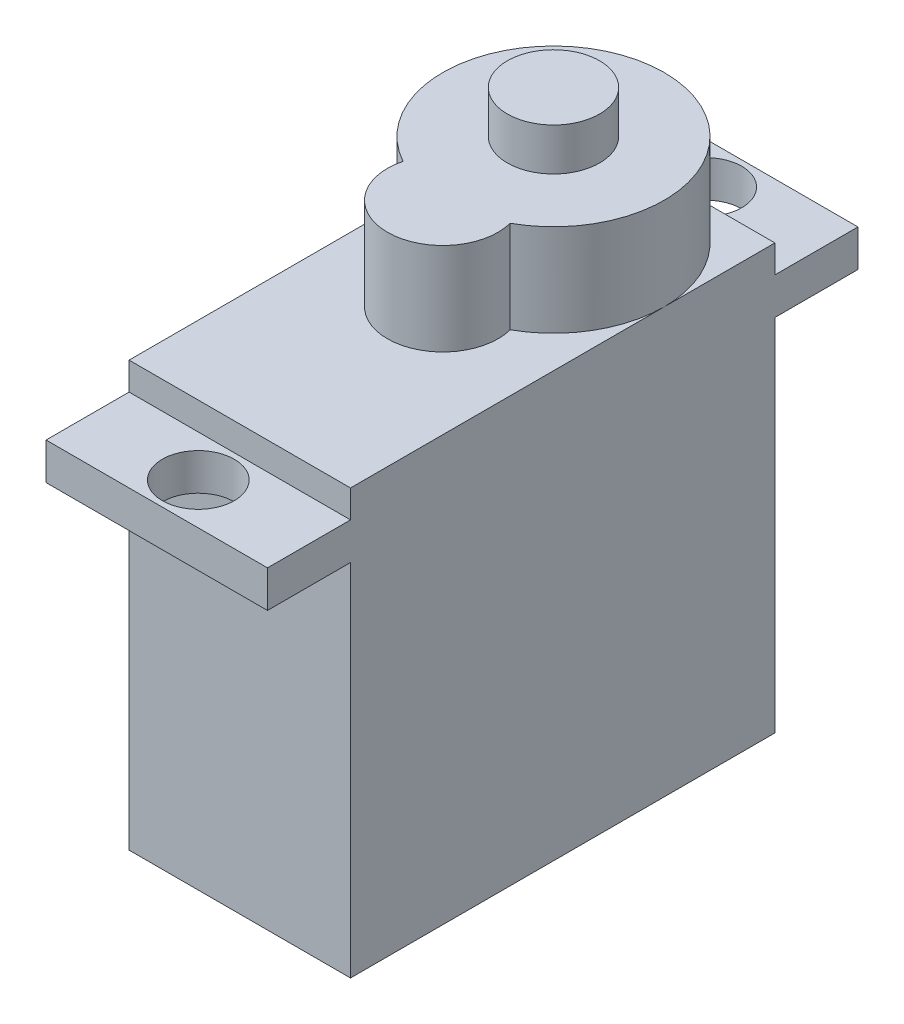
SolidWorks part; units mm, degrees
ref_plane "Plan de face" through (0, 0, 0) normal (0, 0, 1) x (1, 0, 0)
ref_plane "Plan de dessus" through (0, 0, 0) normal (0, 1, 0) x (1, 0, 0)
ref_plane "Plan de droite" through (0, 0, 0) normal (1, 0, 0) x (0, 0, -1)
sketch "Esquisse1" plane through (0, 0, 0) normal (0, 1, 0) x (1, 0, 0)
  line L0 (0, 30.9153) -> (0, -30.9153) construction
  line L1 (-6, 6) -> (6, 6)
  line L2 (-6, 6) -> (-6, -17)
  line L3 (-6, -17) -> (6, -17)
  line L4 (6, 6) -> (6, -17)
  dimension "D1" = 12
  dimension "D2" = 23
  dimension "D3" = 6
extrude "Boss.-Extru.1" add sketch "Esquisse1" against normal blind 19.5 and the other way blind 3.5
sketch "Esquisse2" plane through (0, 0, 0) normal (0, 1, 0) x (1, 0, 0)
  line L0 (-6, 6) -> (-6, -17) construction
  line L1 (-6, 10.5) -> (6, 10.5)
  line L2 (-6, 10.5) -> (-6, -21.5)
  line L3 (-6, -21.5) -> (6, -21.5)
  line L4 (6, 10.5) -> (6, -21.5)
  line L5 (6, -17) -> (6, 6) construction
  line L6 (-13.5529, -5.5) -> (17.1246, -5.5) construction
  line L7 (6, 6) -> (-6, 6) construction
  line L8 (-6, -17) -> (6, -17) construction
  dimension "D1" = 32
extrude "Boss.-Extru.2" add sketch "Esquisse2" along normal blind 2
sketch "Esquisse3" plane through (0, 3.5, 0) normal (0, 1, 0) x (1, 0, 0)
  line L0 (6, 6) -> (-6, 6) construction
  arc A0 (2.9047, -5.25) -> (-2.9047, -5.25) centre (0, 0) ccw
  arc A1 (-2.9047, -5.25) -> (2.9047, -5.25) centre (0, -6) ccw
  dimension "D1" = 6
extrude "Boss.-Extru.3" add sketch "Esquisse3" along normal blind 5
sketch "Esquisse4" plane through (0, 8.5, 0) normal (0, 1, 0) x (1, 0, 0)
  circle A0 centre (0, 0) radius 2.5
  dimension "D1" = 5
extrude "Boss.-Extru.4" add sketch "Esquisse4" along normal blind 2.3
sketch "Esquisse5" plane through (0, 0, 0) normal (0, 1, 0) x (1, 0, 0)
  line L0 (-12.65, -5.5) -> (8.7288, -5.5) construction
  line L1 (6, 10.5) -> (-6, 10.5) construction
  line L2 (-6, -21.5) -> (6, -21.5) construction
  circle A0 centre (0, -19.25) radius 1.95
  circle A1 centre (0, 8.25) radius 1.95
  dimension "D1" = 3.9
  dimension "D2" = 27.5
extrude "Enlèv. mat.-Extru.1" cut sketch "Esquisse5" along normal through all
